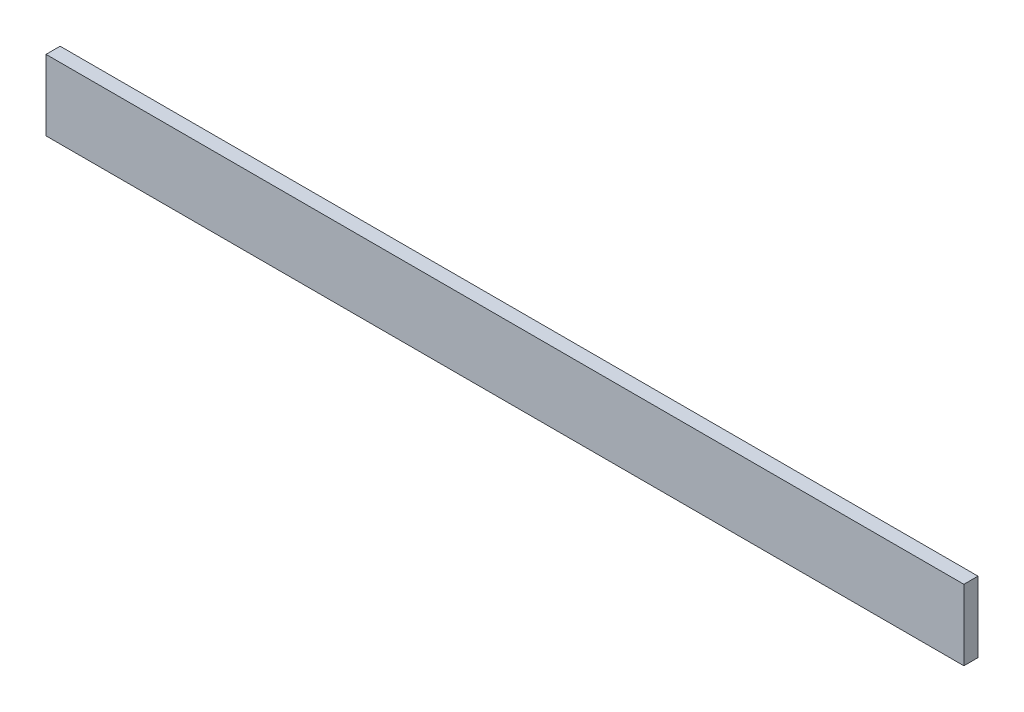
SolidWorks part; units mm, degrees
ref_plane "Спереди" through (0, 0, 0) normal (0, 0, 1) x (1, 0, 0)
ref_plane "Сверху" through (0, 0, 0) normal (0, 1, 0) x (1, 0, 0)
ref_plane "Справа" through (0, 0, 0) normal (1, 0, 0) x (0, 0, -1)
sketch "Эскиз1" plane through (0, 0, 0) normal (1, 0, 0) x (0, 0, -1)
  line L1 (0, 0) -> (10, 0)
  line L2 (0, 0) -> (0, 50)
  line L3 (0, 50) -> (10, 50)
  line L4 (10, 0) -> (10, 50)
extrude "Бобышка-Вытянуть1" add sketch "Эскиз1" along normal blind 650
